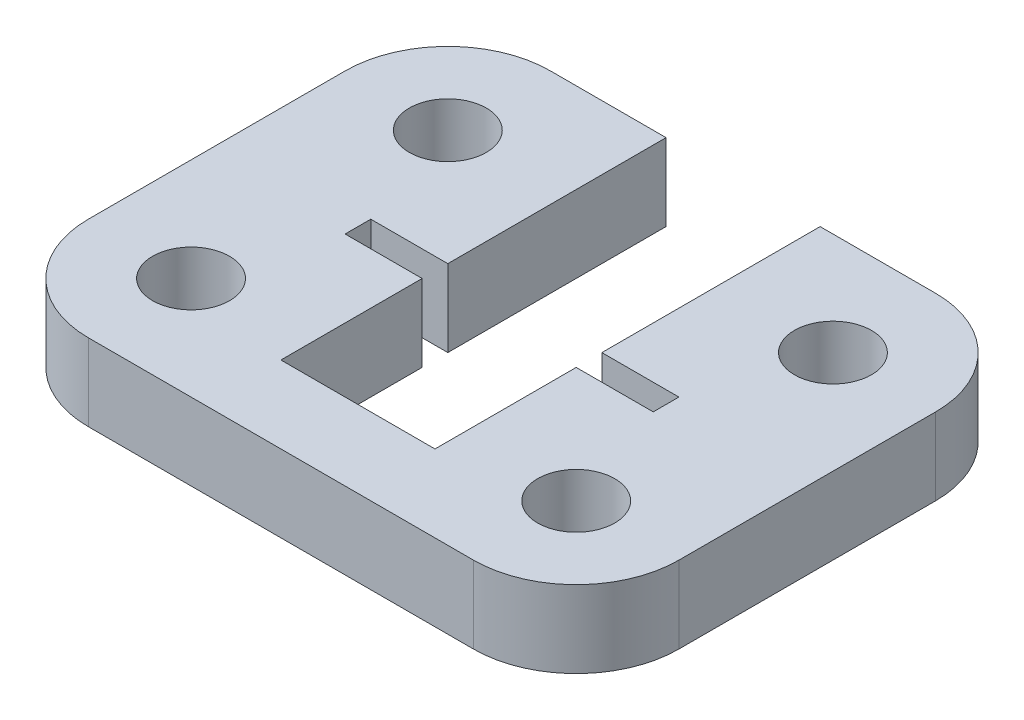
SolidWorks part; units mm, degrees
ref_plane "Front Plane" through (0, 0, 0) normal (0, 0, 1) x (1, 0, 0)
ref_plane "Top Plane" through (0, 0, 0) normal (0, 1, 0) x (1, 0, 0)
ref_plane "Right Plane" through (0, 0, 0) normal (1, 0, 0) x (0, 0, -1)
sketch "Sketch1" plane through (0, 0, 0) normal (0, 1, 0) x (1, 0, 0)
  line L33 (7.9513, -43.5529) -> (7.9513, -52.0529)
  line L34 (7.9513, -52.0529) -> (10.9513, -52.0529)
  line L35 (10.9513, -52.0529) -> (10.9513, -53.0529)
  line L36 (10.9513, -53.0529) -> (7.9513, -53.0529)
  line L37 (7.9513, -53.0529) -> (7.9513, -58.5529)
  line L38 (7.9513, -58.5529) -> (1.9513, -58.5529)
  line L39 (1.9513, -58.5529) -> (1.9513, -53.0529)
  line L40 (1.9513, -53.0529) -> (-1.0487, -53.0529)
  line L41 (-1.0487, -53.0529) -> (-1.0487, -52.0529)
  line L42 (-1.0487, -52.0529) -> (1.9513, -52.0529)
  line L43 (1.9513, -52.0529) -> (1.9513, -43.5529)
  line L44 (1.9513, -43.5529) -> (-2.5487, -43.5529)
  line L45 (-6.5487, -47.5529) -> (-6.5487, -57.5529)
  line L46 (-2.5487, -61.5529) -> (12.4513, -61.5529)
  line L47 (16.4513, -57.5529) -> (16.4513, -47.5529)
  line L48 (12.4513, -43.5529) -> (7.9513, -43.5529)
  arc A63 (-2.5487, -43.5529) -> (-6.5487, -47.5529) centre (-2.5487, -47.5529) ccw
  arc A64 (-6.5487, -57.5529) -> (-2.5487, -61.5529) centre (-2.5487, -57.5529) ccw
  arc A65 (12.4513, -61.5529) -> (16.4513, -57.5529) centre (12.4513, -57.5529) ccw
  arc A66 (16.4513, -47.5529) -> (12.4513, -43.5529) centre (12.4513, -47.5529) ccw
  circle A67 centre (12.4513, -47.5529) radius 1.5
  circle A68 centre (12.4513, -57.5529) radius 1.5
  circle A69 centre (-2.5487, -57.5529) radius 1.5
  circle A70 centre (-2.5487, -47.5529) radius 1.5
extrude "Boss-Extrude1" add sketch "Sketch1" along normal blind 3
